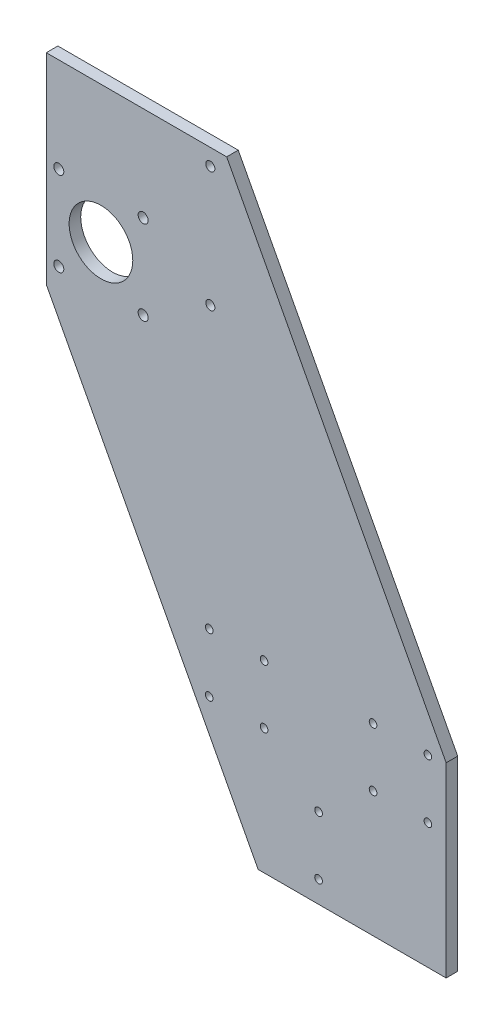
SolidWorks part; units mm, degrees
material "Acero al carbono no aleado"
ref_plane "Alzado" through (0, 0, 0) normal (0, 0, 1) x (1, 0, 0)
ref_plane "Planta" through (0, 0, 0) normal (0, 1, 0) x (1, 0, 0)
ref_plane "Vista lateral" through (0, 0, 0) normal (1, 0, 0) x (0, 0, -1)
sketch "Croquis1" plane through (0, 0, 0) normal (0, 0, 1) x (1, 0, 0)
  line L0 (-70, 81.05) -> (-70, 36.05) construction
  line L2 (0, 0) -> (0, 82.3899)
  line L3 (-120.4218, 310.1425) -> (-219.4008, 310.1425)
  line L4 (-219.4008, 200) -> (-219.4008, 310.1425)
  line L5 (-140.1813, 65) -> (9.4988, 65) construction
  line L6 (-140, 81.05) -> (-140, 48.95) construction
  line L7 (-58.7594, 81.05) -> (10.3776, 81.05) construction
  line L9 (0, 82.3899) -> (-120.4218, 310.1425)
  line L11 (0, 0) -> (0, -19.8575)
  line L12 (0, -19.8575) -> (-103.1535, -19.8575)
  line L14 (-103.1535, -19.8575) -> (33.9554, -19.8575) construction
  line L15 (-219.4008, 200) -> (-103.1535, -19.8575)
  line L16 (-70, 24.15) -> (-70, -7.95) construction
  circle A0 centre (-40.1, 81.05) radius 2.1
  circle A1 centre (-10, 81.05) radius 2.1
  circle A2 centre (-10, 48.95) radius 2.1
  circle A3 centre (-40.1, 48.95) radius 2.1
  circle A4 centre (-130, 81.05) radius 2.1
  circle A5 centre (-99.9, 81.05) radius 2.1
  circle A6 centre (-99.9, 48.95) radius 2.1
  circle A7 centre (-130, 48.95) radius 2.1
  circle A8 centre (-70, 24.15) radius 2.1
  circle A9 centre (-70, -7.95) radius 2.1
  point P37 (-70, 8.1)
  dimension "D7" = 56.9
  dimension "D4" = 4.2
  dimension "D5" = 4.2
  dimension "D10" = 10
  dimension "D12" = 70
  dimension "D2" = 330
  dimension "D3" = 30.1
  dimension "D6" = 32.1
  dimension "D8" = 10
  dimension "D9" = 70
  dimension "D11" = 140
extrude "Saliente-Extruir1" add sketch "Croquis1" along normal blind 6.35
sketch "Croquis2" plane through (0, 0, 6.35) normal (0, 0, 1) x (1, 0, 0)
  line L0 (-189.4008, 126.4955) -> (-189.4008, -10.042) construction
  line L1 (-155.1031, 235.1425) -> (14.7181, 235.1425) construction
  line L2 (-120.4218, 310.1425) -> (-219.4008, 310.1425) construction
  line L3 (-157.9676, 258.2875) -> (11.8273, 258.2875) construction
  line L4 (-129.4008, 275.1371) -> (-129.4008, 193.6539) construction
  line L5 (-219.4008, 310.1425) -> (-219.4008, 200) construction
  line L6 (-138.0031, 260.1425) -> (5.5508, 260.1425) construction
  circle A1 centre (-212.5458, 258.2875) radius 2.75
  circle A2 centre (-212.5458, 211.9975) radius 2.75
  circle A3 centre (-166.2558, 211.9975) radius 2.75
  circle A4 centre (-166.2558, 258.2875) radius 2.75
  circle A5 centre (-189.4008, 235.1425) radius 17.4625
  circle A6 centre (-129.4008, 235.1425) radius 2.5
  circle A7 centre (-129.4008, 301.1425) radius 2.5
  dimension "D5" = 5.5
  dimension "D7" = 60
  dimension "D8" = 5
  dimension "D9" = 66
  dimension "D1" = 75
  dimension "D2" = 30
  dimension "D3" = 23.145
  dimension "D4" = 23.145
  dimension "D6" = 50
extrude "Cortar-Extruir1" cut sketch "Croquis2" against normal blind 12.7
